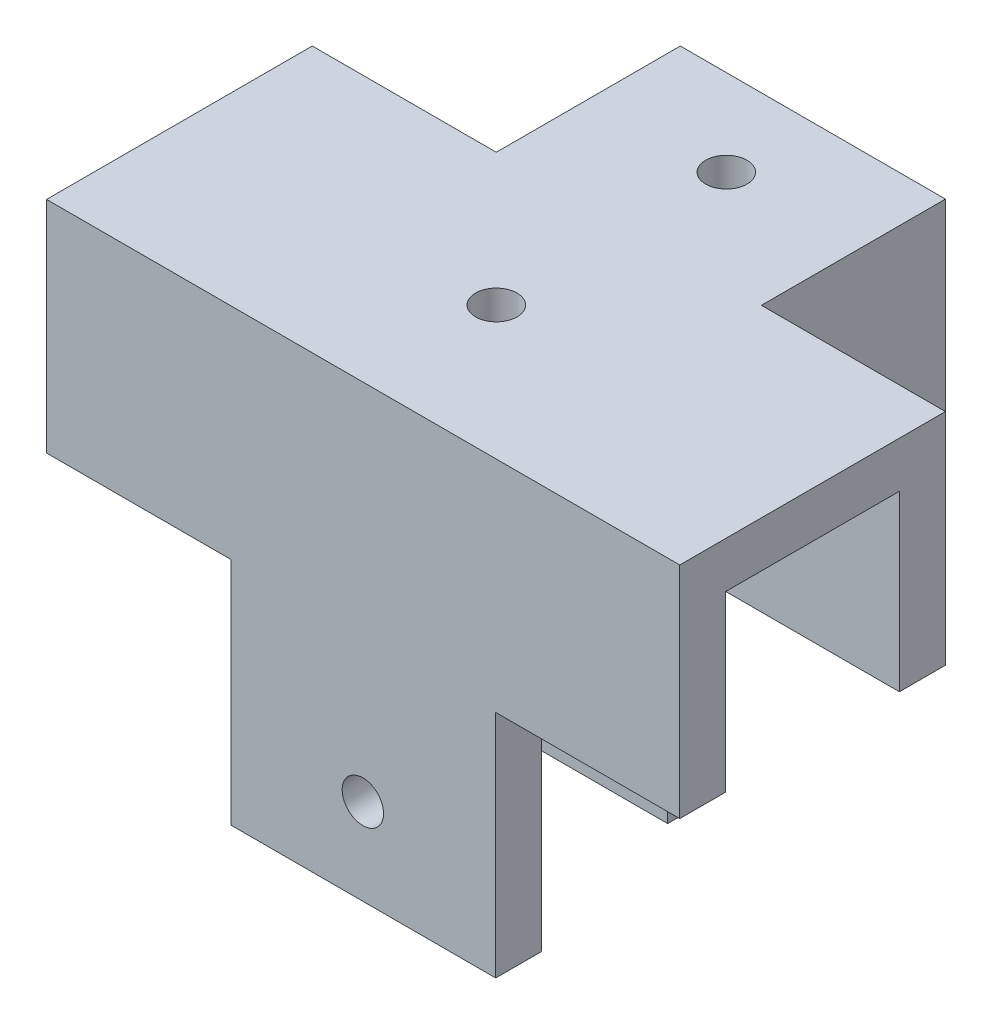
SolidWorks part; units mm, degrees
ref_plane "前视基准面" through (0, 0, 0) normal (0, 0, 1) x (1, 0, 0)
ref_plane "上视基准面" through (0, 0, 0) normal (0, 1, 0) x (1, 0, 0)
ref_plane "右视基准面" through (0, 0, 0) normal (1, 0, 0) x (0, 0, -1)
sketch "草图1" plane through (0, 0, 0) normal (0, 1, 0) x (1, 0, 0)
  line L1 (-22.0308, -9.7154) -> (33.0192, -9.7154)
  line L2 (-22.0308, -9.7154) -> (-22.0308, -13.7154)
  line L3 (-22.0308, -13.7154) -> (33.0192, -13.7154)
  line L4 (33.0192, -9.7154) -> (33.0192, -13.7154)
  line L5 (-22.0308, 9.3846) -> (-6.0308, 9.3846)
  line L6 (-22.0308, 9.3846) -> (-22.0308, 5.3846)
  line L7 (-22.0308, 5.3846) -> (-2.0308, 5.3846)
  line L8 (-2.0308, 9.3846) -> (-2.0308, 5.3846)
  line L9 (-2.0308, 5.3846) -> (-6.0308, 5.3846)
  line L10 (-2.0308, 5.3846) -> (-2.0308, 25.3846)
  line L11 (-2.0308, 25.3846) -> (-6.0308, 25.3846)
  line L12 (-6.0308, 9.3846) -> (-6.0308, 25.3846)
  line L13 (33.0192, 5.3846) -> (13.0192, 5.3846)
  line L14 (33.0192, 5.3846) -> (33.0192, 9.3846)
  line L15 (33.0192, 9.3846) -> (17.0192, 9.3846)
  line L16 (13.0192, 5.3846) -> (13.0192, 8.7692)
  line L17 (13.0192, 5.3846) -> (22.6654, 5.3846)
  line L18 (13.0192, 5.3846) -> (13.0192, 25.3846)
  line L19 (13.0192, 25.3846) -> (17.0192, 25.3846)
  line L20 (17.0192, 9.3846) -> (17.0192, 25.3846)
  dimension "D1" = 4
  dimension "D2" = 4
  dimension "D3" = 4
  dimension "D4" = 4
  dimension "D5" = 4
  dimension "D6" = 15.1
  dimension "D7" = 15.05
  dimension "D8" = 20
  dimension "D9" = 16
  dimension "D10" = 16
  dimension "D11" = 20
  dimension "D12" = 0
  dimension "D13" = 0
extrude "凸台-拉伸1" add sketch "草图1" along normal blind 15.1 contours L12 L5 L6 L7 L8 L10 L11 | L15 L20 L19 L18 L16 L13 L14 | L4 L1 L2 L3
sketch "草图2" plane through (0, 15.1, 0) normal (0, 1, 0) x (1, 0, 0)
  line L1 (-22.0308, 9.3846) -> (33.0192, 9.3846)
  line L2 (-22.0308, 9.3846) -> (-22.0308, -13.7154)
  line L3 (-22.0308, -13.7154) -> (33.0192, -13.7154)
  line L4 (33.0192, 9.3846) -> (33.0192, -13.7154)
  line L5 (-6.0308, 25.3846) -> (17.0192, 25.3846)
  line L6 (-6.0308, 25.3846) -> (-6.0308, 9.3846)
  line L7 (-6.0308, 9.3846) -> (17.0192, 9.3846)
  line L8 (17.0192, 25.3846) -> (17.0192, 9.3846)
  line M1 (-6.0308, 25.3846) -> (-6.0308, 9.3846)
  line M2 (-6.0308, 9.3846) -> (-22.0308, 9.3846)
  line M3 (-22.0308, 9.3846) -> (-22.0308, 5.3846)
  line M4 (-22.0308, 5.3846) -> (-2.0308, 5.3846)
  line M5 (-2.0308, 5.3846) -> (-2.0308, 25.3846)
  line M6 (-2.0308, 25.3846) -> (-6.0308, 25.3846)
extrude "凸台-拉伸2" add sketch "草图2" along normal blind 4 contours L1 M1 M5 M6 | L8 L5 L1 M5 | L4 L1 L2 L3 M5 M4 | L1 M2 M3 M4 M5
sketch "草图3" plane through (0, 0, 0) normal (0, -1, 0) x (1, 0, 0)
  line L0 (-22.0308, 13.7154) -> (33.0192, 13.7154) construction
  line L1 (12.8692, -9.3846) -> (-5.9808, -9.3846)
  line L3 (17.0192, 13.7154) -> (-5.9808, 13.7154)
  line L4 (-5.9808, -9.3846) -> (-5.9808, 13.7154)
  line L5 (-22.0308, 9.7154) -> (33.0192, 9.7154) construction
  line L6 (12.8692, -5.3846) -> (-2.1308, -5.3846)
  line L8 (13.0192, 9.7154) -> (-2.1308, 9.7154)
  line L9 (-2.1308, -5.3846) -> (-2.1308, 9.7154)
  line L12 (13.0192, 9.7154) -> (17.0192, 9.7154)
  line L13 (17.0192, 9.7154) -> (17.0192, 13.7154)
  line L15 (12.8692, -9.3846) -> (12.8692, -5.3846)
  dimension "D1" = 15
extrude "凸台-拉伸3" add sketch "草图3" along normal blind 20
sketch "草图4" plane through (0, 19.1, 0) normal (0, 1, 0) x (1, 0, 0)
  line L0 (17.0192, 25.3846) -> (-6.0308, 25.3846) construction
  circle A0 centre (5.4692, 17.8846) radius 1.8
  circle A1 centre (5.4692, -2.1154) radius 1.8
  dimension "D1" = 3.6
  dimension "D2" = 3.6
  dimension "D3" = 7.5
extrude "切除-拉伸1" cut sketch "草图4" against normal blind 20
sketch "草图5" plane through (0, 0, 13.7154) normal (0, 0, 1) x (1, 0, 0)
  line L0 (17.0192, -20) -> (-5.9808, -20) construction
  circle A0 centre (5.4692, -12.5) radius 1.8
  dimension "D1" = 3.6
  dimension "D2" = 7.5
extrude "切除-拉伸2" cut sketch "草图5" against normal blind 27
